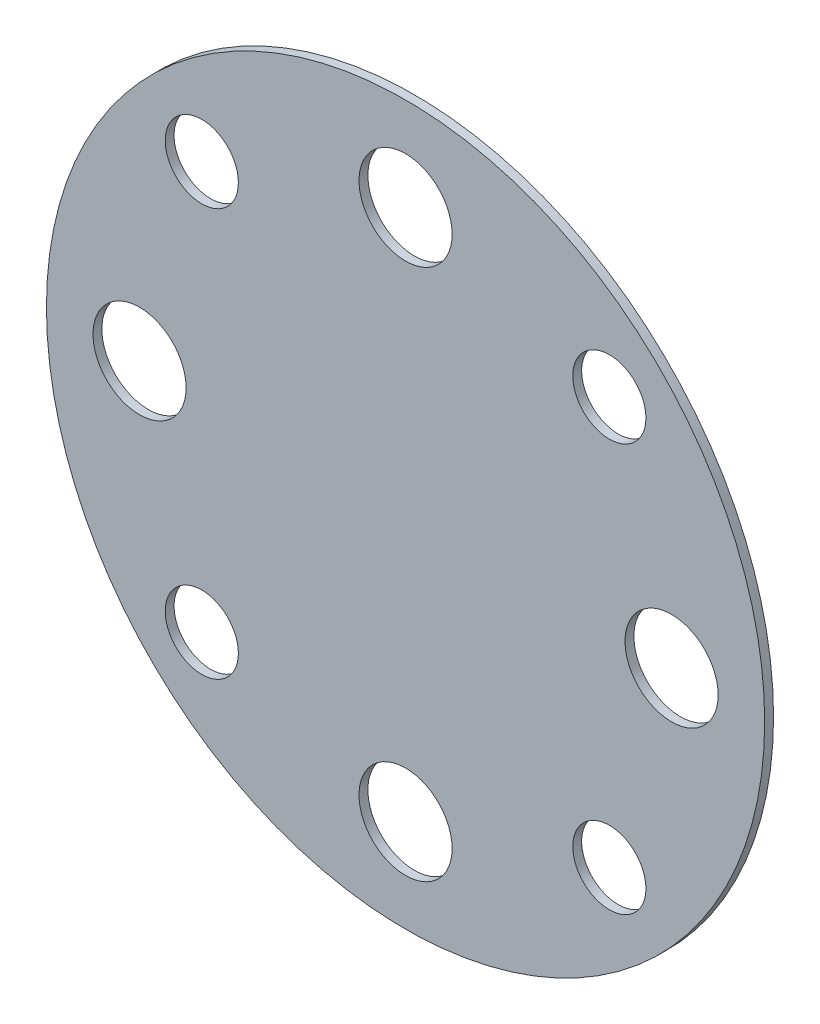
SolidWorks part; units mm, degrees
ref_plane "Front Plane" through (0, 0, 0) normal (1, 0, 0) x (0, 1, 0)
ref_plane "Top Plane" through (0, 0, 0) normal (0, 0, 1) x (0, 1, 0)
ref_plane "Right Plane" through (0, 0, 0) normal (0, 1, 0) x (-1, 0, 0)
sketch "Sketch1" plane through (0, 0, 0) normal (0, 0, 1) x (0, 1, 0)
  line L0 (0, 0) -> (9.1924, 9.1924) construction
  line L1 (0, 0) -> (16.2, 0) construction
  circle A0 centre (0, 0) radius 16.2
  circle A1 centre (0, 0) radius 13 construction
  circle A2 centre (0, 0) radius 12 construction
  circle A3 centre (0, 12) radius 2.1
  circle A4 centre (9.1924, 9.1924) radius 1.65
  circle A5 centre (12, 0) radius 2.1
  circle A6 centre (9.1924, -9.1924) radius 1.65
  circle A7 centre (0, -12) radius 2.1
  circle A8 centre (-9.1924, -9.1924) radius 1.65
  circle A9 centre (-12, 0) radius 2.1
  circle A10 centre (-9.1924, 9.1924) radius 1.65
  dimension "D1" = 32.4
  dimension "D2" = 26
  dimension "D3" = 24
  dimension "D4" = 4.2
  dimension "D5" = 3.3
  dimension "D6" = 45
  dimension "D7" = 4
extrude "Boss-Extrude1" add sketch "Sketch1" along normal blind 0.4
